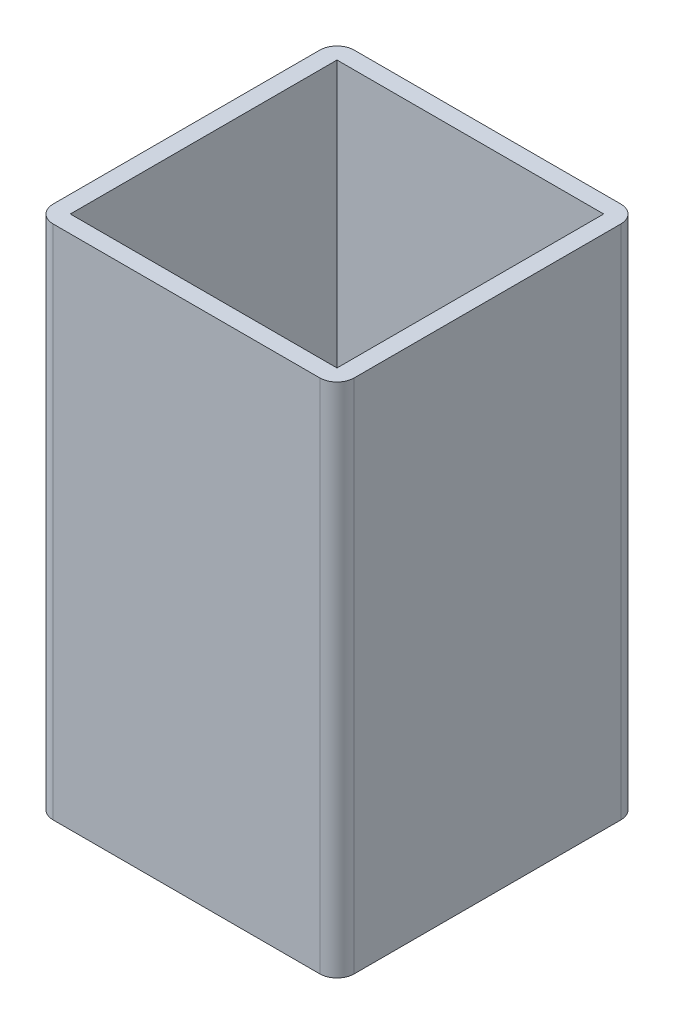
SolidWorks part; units mm, degrees
ref_plane "Front Plane" through (0, 0, 0) normal (0, 0, 1) x (1, 0, 0)
ref_plane "Top Plane" through (0, 0, 0) normal (0, 1, 0) x (1, 0, 0)
ref_plane "Right Plane" through (0, 0, 0) normal (1, 0, 0) x (0, 0, -1)
sketch "Sketch1" plane through (0, 0, 0) normal (0, 1, 0) x (1, 0, 0)
  line L0 (0, 17.5) -> (35, 17.5) construction
  line L1 (2, 0) -> (33, 0)
  line L2 (0, 2) -> (0, 33)
  line L3 (2, 35) -> (33, 35)
  line L4 (35, 2) -> (35, 33)
  line L5 (17.5, 35) -> (17.5, 0) construction
  circle A0 centre (7.5, 17.5) radius 4.75
  circle A1 centre (27.5, 17.5) radius 4.75
  arc A2 (2, 35) -> (0, 33) centre (2, 33) ccw
  arc A3 (0, 2) -> (2, 0) centre (2, 2) ccw
  arc A4 (33, 35) -> (35, 33) centre (33, 33) cw
  arc A5 (35, 2) -> (33, 0) centre (33, 2) cw
  point P17 (0, 0)
  point P22 (35, 0)
  dimension "D2" = 9.5
  dimension "D4" = 2
  dimension "D5" = 2
  dimension "D1" = 35
  dimension "D3" = 20
extrude "Boss-Extrude1" add sketch "Sketch1" along normal blind 60
sketch "Sketch2" plane through (0, 60, 0) normal (0, 1, 0) x (1, 0, 0)
  line L8 (2, 33) -> (2, 2)
  line L9 (2, 2) -> (33, 2)
  line L10 (33, 2) -> (33, 33)
  line L11 (33, 33) -> (2, 33)
  line L12 (2, 33) -> (2, 2)
  line L13 (2, 2) -> (33, 2)
  line L14 (33, 2) -> (33, 33)
  line L15 (33, 33) -> (2, 33)
  dimension "D1" = 2
extrude "Cut-Extrude1" cut sketch "Sketch2" against normal offset from surface (55 mm away) 5 up to face at (17.5, 0, -17.5)
